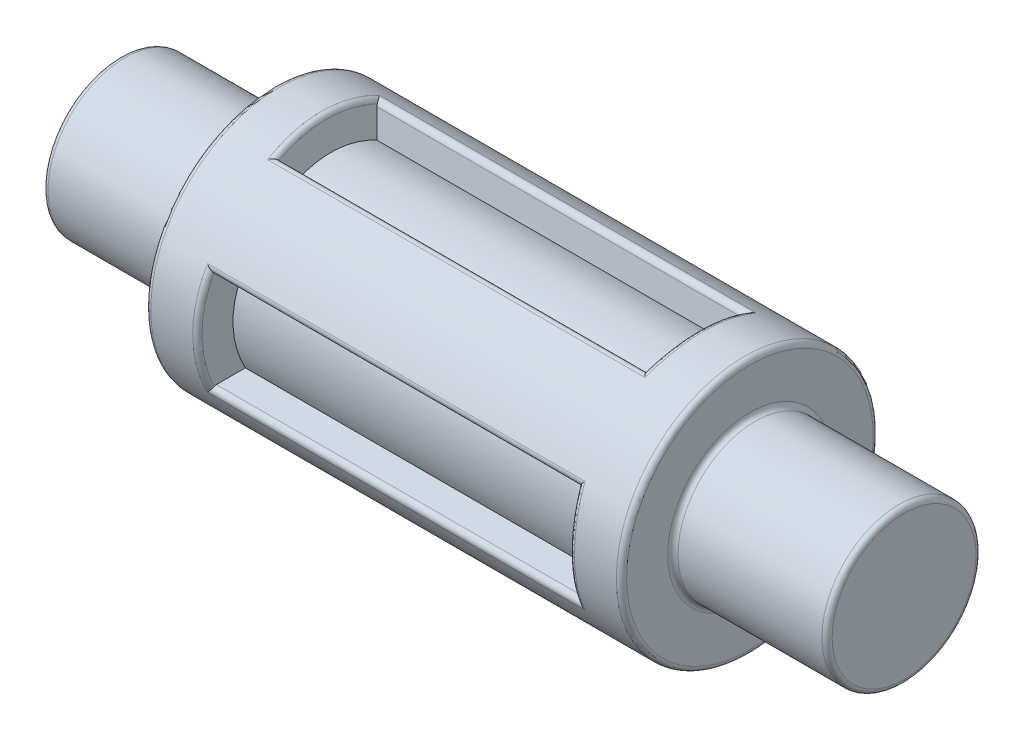
SolidWorks part; units mm, degrees
ref_plane "Front Plane" through (0, 0, 0) normal (0, 0, 1) x (1, 0, 0)
ref_plane "Top Plane" through (0, 0, 0) normal (0, 1, 0) x (1, 0, 0)
ref_plane "Right Plane" through (0, 0, 0) normal (1, 0, 0) x (0, 0, -1)
sketch "Sketch1" plane through (0, 0, 0) normal (0, 1, 0) x (1, 0, 0)
  line L0 (0, 0) -> (50000, 0) construction
  line L1 (0, 0) -> (0, 1.5)
  line L2 (0, 1.5) -> (3, 1.5)
  line L3 (3, 1.5) -> (3, 2.5)
  line L4 (3, 2.5) -> (12.26, 2.5)
  line L5 (12.26, 2.5) -> (12.26, 1.5)
  line L6 (12.26, 1.5) -> (15.26, 1.5)
  line L7 (15.26, 1.5) -> (15.26, 0)
  line L8 (15.26, 0) -> (0, 0)
  dimension "D1" = 9.26
  dimension "D2" = 3
  dimension "D3" = 3
  dimension "D4" = 5
revolve "Revolve1" add sketch "Sketch1" angle 360 about L0
fillet "Fillet1" radius 0.1 6 edges at (12.26, 0, 1.5) (12.26, 0, 2.5) (15.26, 0, 1.5) (3, 0, 2.5) (3, 0, 1.5) (0, 0, 1.5)
ref_plane "Plane1" through (0, 2.5, 0) normal (0, 1, 0) x (-1, 0, 0)
sketch "Sketch2" plane through (0, 2.5, 0) normal (0, 1, 0) x (-1, 0, 0)
  line L0 (-12.26, 2.4) -> (-12.26, -2.4) construction
  line L1 (-11.26, -1) -> (-4, -1)
  line L2 (-11.26, -1) -> (-11.26, 1)
  line L3 (-11.26, 1) -> (-4, 1)
  line L4 (-4, -1) -> (-4, 1)
  line L5 (-11.26, -1) -> (-4, 1) construction
  line L6 (-11.26, 1) -> (-4, -1) construction
  line L7 (-3, -2.4) -> (-3, 2.4) construction
  point P0 (-7.63, 0)
  dimension "D1" = 1
  dimension "D2" = 1
  dimension "D3" = 2
extrude "Cut-Extrude1" cut sketch "Sketch2" against normal blind 0.8 draft 10
fillet "Fillet2" radius 0.1 4 edges at (4, 2.5, 0) (7.63, 2.3059, 0.9658) (7.63, 2.3059, -0.9658) (11.26, 2.5, 0)
pattern_circular "CirPattern1" count 4 over 360 about axis through (3, 0, 0) along (1, 0, 0) of "Cut-Extrude1", "Fillet2"
sketch "Sketch3" plane through (3, 0, 0) normal (-1, 0, 0) x (0, 0, 1)
  circle A0 centre (0, 0) radius 1.9047
extrude "Boss-Extrude1" add sketch "Sketch3" against normal up to surface (9.26 mm away) up to face at (12.26, 0, 1.6)
